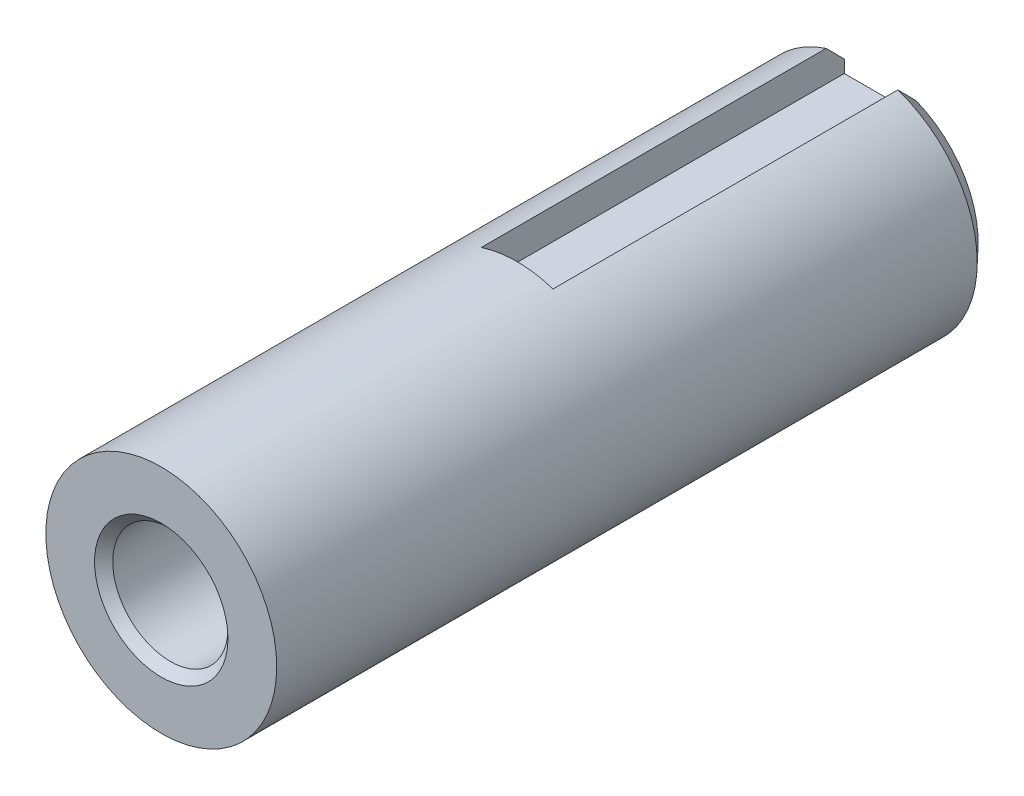
SolidWorks part; units mm, degrees
material "ASTM A36 Acero"
ref_plane "Alzado" through (0, 0, 0) normal (0, 0, 1) x (1, 0, 0)
ref_plane "Planta" through (0, 0, 0) normal (0, 1, 0) x (1, 0, 0)
ref_plane "Vista lateral" through (0, 0, 0) normal (1, 0, 0) x (0, 0, -1)
sketch "Croquis3" plane through (0, 0, 0) normal (0, 0, 1) x (1, 0, 0)
  circle A0 centre (0, 0) radius 6.36
extrude "Saliente-Extruir2" add sketch "Croquis3" against normal blind 39.6
sketch "Croquis4" plane through (0, 0, 0) normal (0, 0, 1) x (1, 0, 0)
  circle A0 centre (0, 0) radius 3.175
extrude "Cortar-Extruir1" cut sketch "Croquis4" against normal blind 19.3
sketch "Croquis6" plane through (0, 0, -39.6) normal (0, 0, -1) x (-1, 0, 0)
  line L0 (-1.985, 4.35) -> (1.965, 4.35)
  line L3 (-1.985, 4.35) -> (-1.985, 6.744)
  line L4 (-1.985, 6.744) -> (1.965, 6.744)
  line L5 (1.965, 6.744) -> (1.965, 4.35)
extrude "Cortar-Extruir3" cut sketch "Croquis6" against normal blind 20
chamfer "Chaflán1" distance 0.95 distance2 1 1 edges at (-0.0105, -6.36, -39.6)
chamfer "Chaflán2" distance 0.5 distance2 0.5 1 edges at (3.175, 0, 0)
